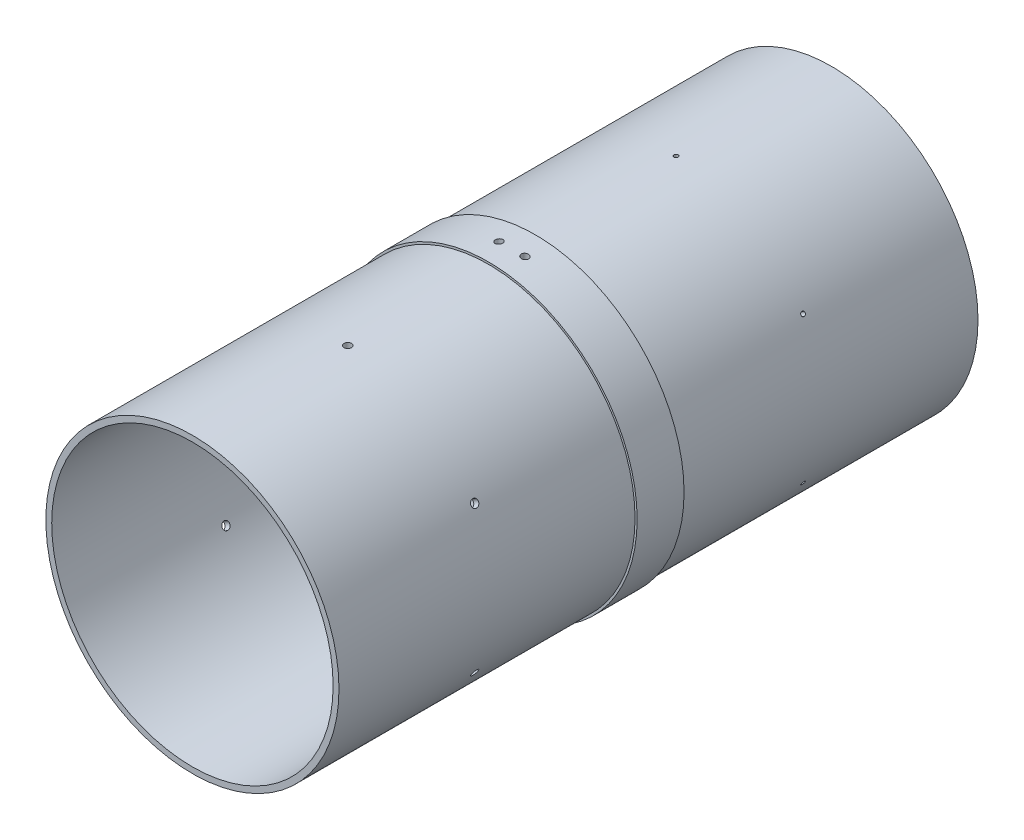
SolidWorks part; units mm, degrees
ref_plane "Front Plane" through (0, 0, 0) normal (0, 0, 1) x (1, 0, 0)
ref_plane "Top Plane" through (0, 0, 0) normal (0, 1, 0) x (1, 0, 0)
ref_plane "Right Plane" through (0, 0, 0) normal (1, 0, 0) x (0, 0, -1)
sketch "Sketch1" plane through (0, 0, 0) normal (0, 0, 1) x (1, 0, 0)
  circle A0 centre (0, 0) radius 79.375
  circle A1 centre (0, 0) radius 76.2
  dimension "D1" = 158.75
  dimension "D2" = 3.175
extrude "Boss-Extrude1" add sketch "Sketch1" along normal blind 346.075
ref_plane "Plane1" through (0, 0, 173.0375) normal (0, 0, 1) x (1, 0, 0)
sketch "Sketch2" plane through (0, 0, 173.0375) normal (0, 0, 1) x (1, 0, 0)
  circle A0 centre (0, 0) radius 79.375 construction
  circle A1 centre (0, 0) radius 79.375
  circle A2 centre (0, 0) radius 80.518
extrude "Boss-Extrude2" add sketch "Sketch2" against normal mid plane 25.4
sketch "Sketch5" plane through (0, 0, 173.0375) normal (0, 0, 1) x (1, 0, 0)
  line L0 (0, 0) -> (0, 47.1719) construction
  line L1 (0, 0) -> (7.0176, 80.2116) construction
  circle A1 centre (0, 0) radius 80.518 construction
  dimension "D1" = 5
ref_plane "Plane2" through (7.0176, 80.2116, 0) normal (0.0872, 0.9962, 0) x (0, 0, 1)
hole_wizard "5/32 (0.15625) Diameter Hole1" positions "Sketch9" profile "Sketch10" hole size "5/32" standard "ANSI Inch"
sketch "Sketch9" plane through (7.0176, 80.2116, 0) normal (0.0872, 0.9962, 0) x (0, 0, 1)
  point P0 (173.0375, 0)
sketch "Sketch10" plane through (7.0176, 80.2116, 173.0375) normal (0, 0, 1) x (-0.9962, 0.0872, 0)
  line L0 (0, 0) -> (0, 4.318)
  line L1 (0, 4.318) -> (1.9844, 4.318)
  line L2 (1.9844, 4.318) -> (1.9844, 0)
  line L5 (1.9844, 0) -> (0, 0)
  line L11 (0, -6.35) -> (0, 107.95) construction
  dimension "Thru Hole Dia." = 3.9688
  dimension "Thru Hole Depth" = 4.318
mirror "Mirror1" about plane through (0, 0, 0) normal (1, 0, 0) of "5/32 (0.15625) Diameter Hole1"
ref_plane "Plane3" through (0, 79.375, 0) normal (0, 1, 0) x (1, 0, 0)
sketch "Sketch11" plane through (0, 79.375, 0) normal (0, 1, 0) x (1, 0, 0)
  line L0 (80.518, -160.3375) -> (-80.518, -160.3375) construction
  point P0 (0, -84.1375)
  dimension "D1" = 76.2
hole_wizard "#4-40 Tapped Hole1" positions "Sketch12" profile "Sketch13" tap size "#4-40" standard "ANSI Inch"
sketch "Sketch12" plane through (0, 79.375, 0) normal (0, 1, 0) x (1, 0, 0)
  point P0 (0, -84.1375)
sketch "Sketch13" plane through (0, 79.375, 84.1375) normal (1, 0, 0) x (0, 0, 1)
  line L0 (0, 0) -> (0, 3.175)
  line L1 (0, 3.175) -> (1.1303, 3.175)
  line L2 (1.1303, 3.175) -> (1.1303, 0)
  line L5 (1.1303, 0) -> (0, 0)
  line L11 (0, -6.35) -> (0, 107.95) construction
  dimension "Thru Tap Drill Dia." = 2.2606
  dimension "Thru Tap Drill Depth" = 3.175
cosmetic thread "Hole Thread1" parameters "D2"=2.8448
pattern_circular "CirPattern1" count 6 over 360 about axis through (0, 0, 0) along (0, 0, 1) of "#4-40 Tapped Hole1"
cosmetic thread "Hole Thread2" parameters "D2"=2.8448
cosmetic thread "Hole Thread3" parameters "D2"=2.8448
cosmetic thread "Hole Thread4" parameters "D2"=2.8448
cosmetic thread "Hole Thread9" parameters "D2"=2.8448
cosmetic thread "Hole Thread10" parameters "D2"=2.8448
sketch "Sketch14" plane through (0, 79.375, 0) normal (0, 1, 0) x (1, 0, 0)
  line L0 (-79.375, -185.7375) -> (79.375, -185.7375) construction
  point P0 (0, -261.9375)
  dimension "D1" = 76.2
hole_wizard "#10-32 Tapped Hole1" positions "Sketch15" profile "Sketch16" tap size "#10-32" standard "ANSI Inch"
sketch "Sketch15" plane through (0, 79.375, 0) normal (0, 1, 0) x (1, 0, 0)
  point P0 (0, -261.9375)
sketch "Sketch16" plane through (0, 79.375, 261.9375) normal (1, 0, 0) x (0, 0, 1)
  line L0 (0, 0) -> (0, 3.175)
  line L1 (0, 3.175) -> (2.0193, 3.175)
  line L2 (2.0193, 3.175) -> (2.0193, 0)
  line L5 (2.0193, 0) -> (0, 0)
  line L11 (0, -6.35) -> (0, 107.95) construction
  dimension "Thru Tap Drill Dia." = 4.0386
  dimension "Thru Tap Drill Depth" = 3.175
cosmetic thread "Hole Thread5" parameters "D2"=4.826
pattern_circular "CirPattern2" count 6 over 360 about axis through (0, 0, 346.075) along (0, 0, 1) of "#10-32 Tapped Hole1"
cosmetic thread "Hole Thread6" parameters "D2"=4.826
cosmetic thread "Hole Thread7" parameters "D2"=4.826
cosmetic thread "Hole Thread8" parameters "D2"=4.826
cosmetic thread "Hole Thread11" parameters "D2"=4.826
cosmetic thread "Hole Thread12" parameters "D2"=4.826
